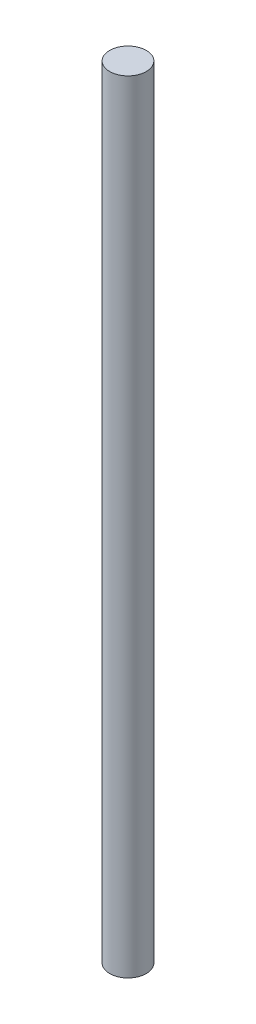
SolidWorks part; units mm, degrees
ref_plane "Front Plane" through (0, 0, 0) normal (0, 0, 1) x (1, 0, 0)
ref_plane "Top Plane" through (0, 0, 0) normal (0, 1, 0) x (1, 0, 0)
ref_plane "Right Plane" through (0, 0, 0) normal (1, 0, 0) x (0, 0, -1)
sketch "Sketch1" plane through (0, 0, 0) normal (0, 1, 0) x (1, 0, 0)
  circle A0 centre (0, 0) radius 2.3813
  dimension "D1" = 4.7625
extrude "Boss-Extrude1" add sketch "Sketch1" along normal blind 101.6
